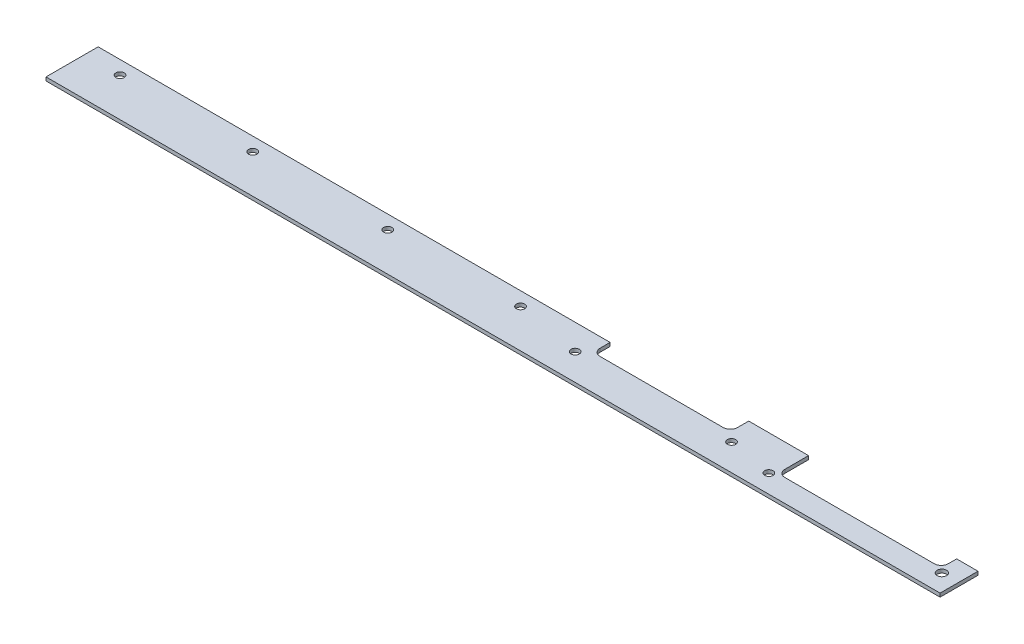
SolidWorks part; units mm, degrees
material "Простая углеродистая сталь"
ref_plane "Спереди" through (0, 0, 0) normal (0, 0, 1) x (1, 0, 0)
ref_plane "Сверху" through (0, 0, 0) normal (0, 1, 0) x (1, 0, 0)
ref_plane "Справа" through (0, 0, 0) normal (1, 0, 0) x (0, 0, -1)
sketch "Эскиз1" plane through (0, 0, 0) normal (0, 1, 0) x (1, 0, 0)
  line L0 (299.3, 22.5) -> (299.3, 12.5)
  line L1 (0, 0) -> (377.3, 0)
  line L2 (0, 0) -> (0, 22)
  line L5 (302.3, 9.5) -> (365.3, 9.5)
  line L7 (368.3, 12.5) -> (368.3, 16)
  line L8 (368.3, 16) -> (377.3, 16)
  line L9 (377.3, 16) -> (377.3, 0)
  line L10 (184, 11.25) -> (274.3, 11.25) construction
  line L11 (0, 22) -> (216.05, 22)
  line L12 (216.05, 22) -> (216.05, 17.75)
  line L14 (299.3, 22.5) -> (274.05, 22.5)
  line L15 (274.05, 22.5) -> (274.05, 17.75)
  line L16 (271.05, 14.75) -> (219.05, 14.75)
  line L17 (291.7138, 7.75) -> (374.9796, 7.75) construction
  line L18 (6.9438, 16.25) -> (188.9185, 16.25) construction
  circle A1 centre (297.3, 7.75) radius 1.75
  circle A2 centre (71, 16.25) radius 1.75
  circle A3 centre (15, 16.25) radius 1.75
  circle A4 centre (128, 16.25) radius 1.75
  circle A5 centre (184, 16.25) radius 1.75
  circle A8 centre (370.3, 7.75) radius 2
  arc A9 (299.3, 12.5) -> (302.3, 9.5) centre (302.3, 12.5) ccw
  arc A10 (365.3, 9.5) -> (368.3, 12.5) centre (365.3, 12.5) ccw
  circle A11 centre (212.05, 11.25) radius 1.75
  circle A12 centre (278.05, 11.25) radius 1.75
  arc A13 (274.05, 17.75) -> (271.05, 14.75) centre (271.05, 17.75) cw
  arc A14 (216.05, 17.75) -> (219.05, 14.75) centre (219.05, 17.75) ccw
  point P31 (0, 0)
  point P35 (0, 0)
  point P36 (0, 0)
  point P37 (0, 0)
  point P40 (0, 0)
  point P41 (0, 0)
  dimension "D2" = 3
  dimension "D3" = 3
  dimension "D4" = 4
  dimension "D7" = 3
  dimension "D1" = 4
  dimension "D5" = 11.25
  dimension "D6" = 7.75
extrude "Бобышка-Вытянуть1" add sketch "Эскиз1" along normal blind 1.5 contours L2 L1
